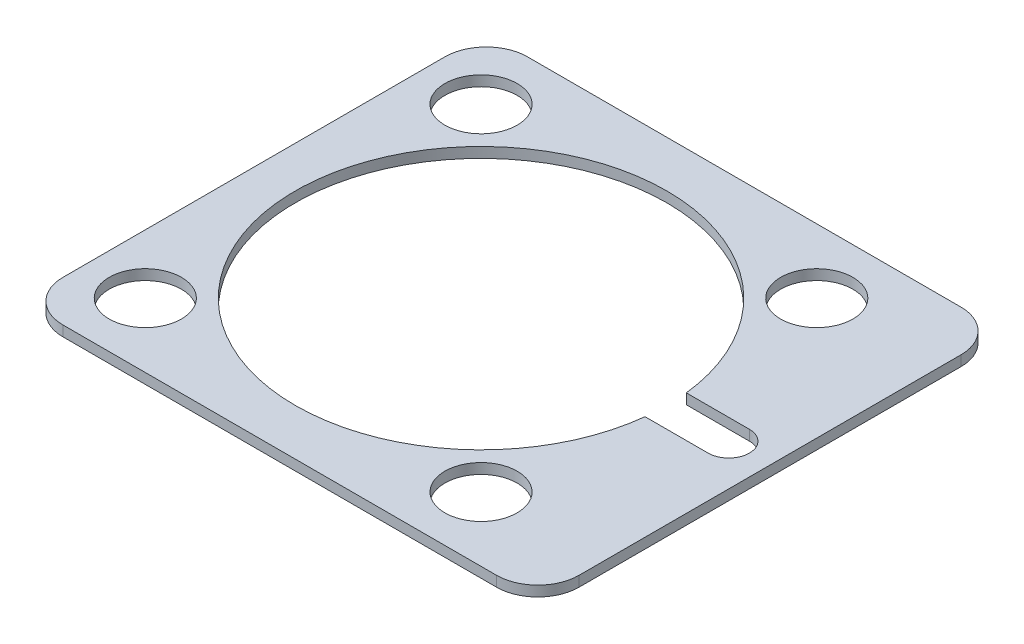
SolidWorks part; units mm, degrees
material "Rubber"
ref_plane "Front Plane" through (0, 0, 0) normal (0, 0, 1) x (1, 0, 0)
ref_plane "Top Plane" through (0, 0, 0) normal (0, 1, 0) x (1, 0, 0)
ref_plane "Right Plane" through (0, 0, 0) normal (1, 0, 0) x (0, 0, -1)
sketch "Sketch1" plane through (0, 0, 0) normal (0, 1, 0) x (1, 0, 0)
  line L1 (28, -22.5) -> (-22, -22.5)
  line L2 (28, -22.5) -> (28, 22.5)
  line L3 (28, 22.5) -> (-22, 22.5)
  line L4 (-22, -22.5) -> (-22, 22.5)
  line L5 (28, -22.5) -> (-22, 22.5) construction
  line L6 (28, 22.5) -> (-22, -22.5) construction
  point P0 (3, 0)
  dimension "D1" = 50
  dimension "D2" = 45
  dimension "D3" = 22
extrude "Body" add sketch "Sketch1" along normal mid plane 1
sketch "Sketch2" plane through (0, 0.5, 0) normal (0, 1, 0) x (1, 0, 0)
  line L0 (0, 0) -> (29.1829, 0) construction
  line L1 (17.8885, 2) -> (24, 2)
  line L2 (17.8885, -2) -> (24, -2)
  arc A0 (17.8885, 2) -> (17.8885, -2) centre (0, 0) ccw
  arc A1 (24, -2) -> (24, 2) centre (24, 0) ccw
  dimension "D1" = 36
  dimension "D3" = 24
  dimension "D2" = 4
extrude "Center hole" cut sketch "Sketch2" against normal through all
sketch "Sketch3" plane through (0, 0.5, 0) normal (0, 1, 0) x (1, 0, 0)
  line L0 (0, 0) -> (0, 23) construction
  line L1 (0, 0) -> (16.2635, 16.2635) construction
  circle A0 centre (0, 0) radius 23 construction
  circle A1 centre (16.2635, 16.2635) radius 3.5
  dimension "D1" = 46
  dimension "D3" = 7
  dimension "D2" = 45
extrude "Hole 1" cut sketch "Sketch3" against normal through all
pattern_circular "Holes 2-4" count 4 over 360 about axis through (0, 0, 0) along (0, 1, 0) of "Hole 1"
fillet "R4 Fillets" radius 4 4 edges at (-22, 0, -22.5) (28, 0, -22.5) (-22, 0, 22.5) (28, 0, 22.5)
